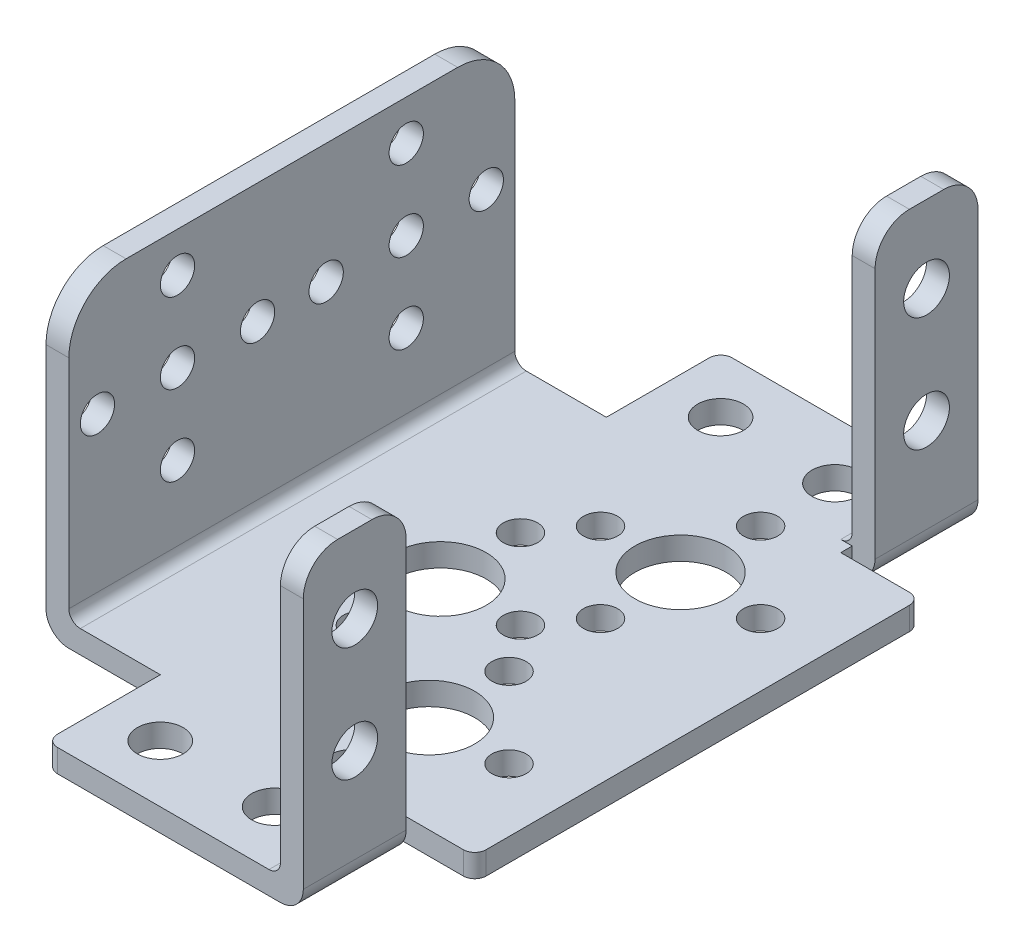
SolidWorks part; units mm, degrees
material "5052-H32"
ref_plane "Front Plane" through (0, 0, 0) normal (0, 0, 1) x (1, 0, 0)
ref_plane "Top Plane" through (0, 0, 0) normal (0, 1, 0) x (1, 0, 0)
ref_plane "Right Plane" through (0, 0, 0) normal (1, 0, 0) x (0, 0, -1)
sketch "Sketch1" plane through (0, 0, 0) normal (0, 1, 0) x (1, 0, 0)
  line L1 (17.745, -19.5) -> (-17.745, -19.5)
  line L2 (17.745, -19.5) -> (17.745, 19.5)
  line L3 (17.745, 19.5) -> (-17.745, 19.5)
  line L4 (-17.745, -19.5) -> (-17.745, 19.5)
  line L5 (17.745, -19.5) -> (-17.745, 19.5) construction
  line L6 (17.745, 19.5) -> (-17.745, -19.5) construction
  point P0 (0, 0)
  dimension "D1" = 39
  dimension "D2" = 35.49
extrude "Boss-Extrude1" add sketch "Sketch1" along normal blind 2
sketch "Sketch2" plane through (0, 2, 0) normal (0, 1, 0) x (1, 0, 0)
  line L0 (17.745, 19.5) -> (-17.745, 19.5) construction
  line L1 (-9.745, 19.5) -> (10.755, 19.5)
  line L2 (-9.745, 19.5) -> (-9.745, 29.5)
  line L3 (-9.745, 29.5) -> (10.755, 29.5)
  line L4 (10.755, 19.5) -> (10.755, 29.5)
  line L5 (-17.745, 19.5) -> (-17.745, -19.5) construction
  line L6 (-17.745, -19.5) -> (17.745, -19.5) construction
  line L7 (-9.745, -19.5) -> (10.755, -19.5)
  line L8 (-9.745, -19.5) -> (-9.745, -29.5)
  line L9 (-9.745, -29.5) -> (10.755, -29.5)
  line L10 (10.755, -19.5) -> (10.755, -29.5)
  dimension "D1" = 29.5
  dimension "D2" = 8
  dimension "D3" = 28.5
  dimension "D4" = 29.5
extrude "Boss-Extrude2" add sketch "Sketch2" against normal blind 2
sketch "Sketch3" plane through (-17.745, 0, 0) normal (-1, 0, 0) x (0, 0, 1)
  line L1 (-19.5, 0) -> (19.5, 0)
  line L2 (-19.5, 0) -> (-19.5, 27)
  line L3 (-19.5, 27) -> (19.5, 27)
  line L4 (19.5, 0) -> (19.5, 27)
  dimension "D1" = 39
  dimension "D2" = 27
extrude "Boss-Extrude3" add sketch "Sketch3" along normal blind 2
sketch "Sketch4" plane through (10.755, 0, 0) normal (1, 0, 0) x (0, 0, -1)
  line L1 (-29.5, 0) -> (-20.5, 0)
  line L2 (-29.5, 0) -> (-29.5, 27)
  line L3 (-29.5, 27) -> (-20.5, 27)
  line L4 (-20.5, 0) -> (-20.5, 27)
  line L5 (29.5, 0) -> (20.5, 0)
  line L6 (29.5, 0) -> (29.5, 27)
  line L7 (29.5, 27) -> (20.5, 27)
  line L8 (20.5, 0) -> (20.5, 27)
  dimension "D1" = 9
  dimension "D2" = 9
extrude "Boss-Extrude4" add sketch "Sketch4" along normal blind 2
sketch "Sketch5" plane through (0, 2, 0) normal (0, 1, 0) x (1, 0, 0)
  line L1 (17.745, -19.5) -> (17.745, 19.5) construction
  line L2 (-9.745, -29.5) -> (10.755, -29.5) construction
  line L3 (-42.7315, 0) -> (38.9034, 0) construction
  circle A0 centre (-4.755, 0) radius 4
  circle A1 centre (5.245, 11) radius 4
  circle A2 centre (5.245, -11) radius 4
  circle A3 centre (-4.755, -24.5) radius 2
  circle A4 centre (5.245, -24.5) radius 2
  circle A5 centre (5.245, 24.5) radius 2
  circle A6 centre (5.245, 18) radius 1.5
  circle A7 centre (12.245, 11) radius 1.5
  circle A8 centre (5.245, 4) radius 1.5
  circle A9 centre (-1.755, 11) radius 1.5
  circle A10 centre (-4.755, 7) radius 1.5
  circle A11 centre (2.245, 0) radius 1.5
  circle A12 centre (-4.755, -7) radius 1.5
  circle A13 centre (-11.755, 0) radius 1.5
  circle A14 centre (5.245, -4) radius 1.5
  circle A15 centre (12.245, -11) radius 1.5
  circle A16 centre (5.245, -18) radius 1.5
  circle A17 centre (-1.755, -11) radius 1.5
  circle A18 centre (-4.755, 24.5) radius 2
  dimension "D2" = 11
  dimension "D3" = 12.5
  dimension "D4" = 12.5
  dimension "D5" = 10
  dimension "D6" = 8
  dimension "D7" = 10
  dimension "D11" = 4
  dimension "D8" = 3
  dimension "D10" = 4
  dimension "D1" = 22
  dimension "D9" = 5
extrude "Cut-Extrude1" cut sketch "Sketch5" against normal blind 2
sketch "Sketch6" plane through (12.755, 0, 0) normal (1, 0, 0) x (0, 0, -1)
  line L0 (-20.5, 27) -> (-29.5, 27) construction
  line L1 (29.5, 27) -> (20.5, 27) construction
  circle A0 centre (-25, 20.25) radius 2
  circle A1 centre (-25, 10.25) radius 2
  circle A2 centre (25, 20.25) radius 2
  circle A3 centre (25, 10.25) radius 2
  point P10 (25, 27)
  dimension "D1" = 4
  dimension "D2" = 4
  dimension "D7" = 4
  dimension "D8" = 4
  dimension "D3" = 6.75
  dimension "D4" = 10
  dimension "D5" = 10
  dimension "D6" = 6.75
extrude "Cut-Extrude2" cut sketch "Sketch6" against normal blind 2
sketch "Sketch7" plane through (-17.745, 0, 0) normal (1, 0, 0) x (0, 0, -1)
  line L1 (-19.5, 2) -> (-19.5, 27) construction
  line L2 (19.5, 27) -> (19.5, 2) construction
  circle A0 centre (-10, 16.5) radius 1.5
  circle A2 centre (-10, 23.5) radius 1.5
  circle A3 centre (-3, 16.5) radius 1.5
  circle A4 centre (-10, 9.5) radius 1.5
  circle A5 centre (-17, 16.5) radius 1.5
  circle A6 centre (10, 16.5) radius 1.5
  circle A8 centre (10, 23.5) radius 1.5
  circle A9 centre (17, 16.5) radius 1.5
  circle A10 centre (10, 9.5) radius 1.5
  circle A11 centre (3, 16.5) radius 1.5
  point P2 (-19.5, 14.5)
  dimension "D1" = 2
  dimension "D2" = 3
  dimension "D5" = 3
  dimension "D6" = 3
  dimension "D3" = 9.5
  dimension "D8" = 9.5
extrude "Cut-Extrude3" cut sketch "Sketch7" against normal blind 2
fillet "Fillet1" radius 2 3 edges at (-19.745, 0, 0) (12.755, 0, -25) (12.755, 0, 25)
fillet "Fillet2" radius 1 7 edges at (-9.745, 1, -29.5) (17.745, 1, -19.5) (17.745, 1, 19.5) (-9.745, 1, 29.5)
fillet "Fillet3" radius 3 4 edges at (11.755, 27, -29.5) (11.755, 27, -20.5) (11.755, 27, 20.5) (11.755, 27, 29.5)
fillet "Fillet4" radius 5 2 edges at (-18.745, 27, -19.5) (-18.745, 27, 19.5)
